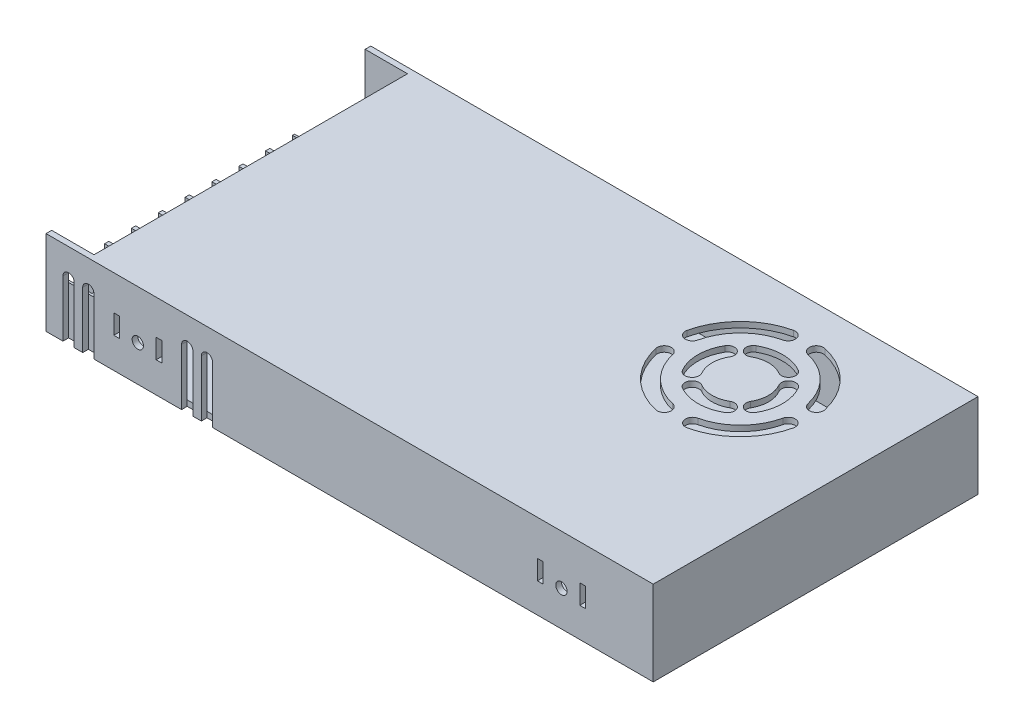
SolidWorks part; units mm, degrees
material "1060 Alloy"
ref_plane "Front Plane" through (0, 0, 0) normal (0, 0, 1) x (1, 0, 0)
ref_plane "Top Plane" through (0, 0, 0) normal (0, 1, 0) x (1, 0, 0)
ref_plane "Right Plane" through (0, 0, 0) normal (1, 0, 0) x (0, 0, -1)
sketch "Sketch1" plane through (0, 0, 0) normal (0, 1, 0) x (1, 0, 0)
  line L1 (107.5, -57.5) -> (-107.5, -57.5)
  line L2 (107.5, -57.5) -> (107.5, 57.5)
  line L3 (107.5, 57.5) -> (-107.5, 57.5)
  line L4 (-107.5, -57.5) -> (-107.5, 57.5)
  line L5 (107.5, -57.5) -> (-107.5, 57.5) construction
  line L6 (107.5, 57.5) -> (-107.5, -57.5) construction
  point P0 (0, 0)
  dimension "D1" = 215
  dimension "D2" = 115
extrude "Boss-Extrude1" add sketch "Sketch1" along normal blind 30
shell "Shell1" thickness 2
sketch "Sketch2" plane through (0, 30, 0) normal (0, 1, 0) x (1, 0, 0)
  line L0 (107.5, -57.5) -> (107.5, 57.5) construction
  line L1 (107.5, 57.5) -> (-107.5, 57.5) construction
  line L2 (60.05, 20.8) -> (14.6527, 20.8) construction
  line L4 (14.6527, 66.1973) -> (60.05, 20.8) construction
  circle A0 centre (60.05, 20.8) radius 12.5 construction
  circle A1 centre (60.05, 20.8) radius 22.5 construction
  arc A2 (53.8, 31.6253) -> (66.3, 31.6253) centre (60.05, 20.8) cw construction
  arc A3 (67.55, 33.7904) -> (52.55, 33.7904) centre (60.05, 20.8) ccw
  arc A4 (65.05, 29.4603) -> (55.05, 29.4603) centre (60.05, 20.8) ccw
  arc A5 (65.05, 29.4603) -> (67.55, 33.7904) centre (66.3, 31.6253) ccw
  arc A6 (52.55, 33.7904) -> (55.05, 29.4603) centre (53.8, 31.6253) ccw
  arc A7 (55.05, 42.7374) -> (38.1126, 25.8) centre (60.05, 20.8) ccw construction
  arc A8 (54.4944, 45.1749) -> (35.6751, 26.3556) centre (60.05, 20.8) ccw
  arc A9 (55.6056, 40.2999) -> (40.5501, 25.2444) centre (60.05, 20.8) ccw
  arc A10 (55.6056, 40.2999) -> (54.4944, 45.1749) centre (55.05, 42.7374) ccw
  arc A11 (35.6751, 26.3556) -> (40.5501, 25.2444) centre (38.1126, 25.8) ccw
  point P9 (60.05, 33.3)
  point P14 (44.1401, 36.7099)
  dimension "D3" = 25
  dimension "D4" = 15
  dimension "D5" = 5
  dimension "D6" = 45
  dimension "D7" = 5
  dimension "D1" = 47.45
  dimension "D2" = 36.7
  dimension "D8" = 45
  dimension "D9" = 5
extrude "Cut-Extrude1" cut sketch "Sketch2" against normal offset from surface (28 mm away) 2 up to face at (0, 0, 0)
pattern_circular "CirPattern1" count 4 over 360 about axis through (60.05, 0, -20.8) along (0, 1, 0) of "Cut-Extrude1"
sketch "Sketch3" plane through (0, 30, 0) normal (0, 1, 0) x (1, 0, 0)
  line L0 (-107.5, 57.5) -> (-107.5, -57.5) construction
  line L1 (-107.5, 55.5) -> (-92.5, 55.5)
  line L2 (-107.5, 55.5) -> (-107.5, -55.5)
  line L3 (-107.5, -55.5) -> (-92.5, -55.5)
  line L4 (-92.5, 55.5) -> (-92.5, -55.5)
  line L5 (107.5, 57.5) -> (-107.5, 57.5) construction
  line L6 (-107.5, -57.5) -> (107.5, -57.5) construction
  dimension "D1" = 2
  dimension "D2" = 2
  dimension "D3" = 15
extrude "Cut-Extrude2" cut sketch "Sketch3" against normal blind 10
sketch "Sketch4" plane through (0, 30, 0) normal (0, 1, 0) x (1, 0, 0)
  line L0 (107.5, -25) -> (-75, -25) construction
  line L1 (107.5, -57.5) -> (107.5, 57.5) construction
  line L2 (-75, -25) -> (-75, 25) construction
  line L3 (-75, 25) -> (107.5, 25) construction
  line L4 (-107.5, -57.5) -> (107.5, -57.5) construction
  line L5 (-107.5, 55.5) -> (-107.5, -55.5) construction
  circle A0 centre (-75, 25) radius 2
  circle A1 centre (-75, -25) radius 2
  circle A3 centre (75, -25) radius 2
  circle A4 centre (75, 25) radius 2
  dimension "D3" = 4
  dimension "D1" = 32.5
  dimension "D2" = 50
  dimension "D4" = 32.5
  dimension "D5" = 150
extrude "Cut-Extrude3" cut sketch "Sketch4" against normal through all from offset 20 offset against normal yes
sketch "Sketch5" plane through (0, 2, 0) normal (0, 1, 0) x (1, 0, 0)
  line L0 (-107, -55.5) -> (-107, -46)
  line L2 (-107, -46) -> (-92.5, -46)
  line L3 (-92.5, -55.5) -> (-92.5, 55.5) construction
  line L4 (-92.5, -46) -> (-92.5, -55.5)
  line L5 (-107.5, -55.5) -> (105.5, -55.5) construction
  line L6 (-92.5, -55.5) -> (-107, -55.5)
  line L7 (-107.5, 55.5) -> (-107.5, -55.5) construction
  dimension "D1" = 9.5
  dimension "D2" = 0.5
extrude "Boss-Extrude2" add sketch "Sketch5" along normal blind 15
sketch "Sketch6" plane through (0, 17, 0) normal (0, 1, 0) x (1, 0, 0)
  line L0 (-107, -46) -> (-107, -55.5) construction
  line L1 (-107, -46.75) -> (-94, -46.75)
  line L2 (-107, -46.75) -> (-107, -54.75)
  line L3 (-107, -54.75) -> (-94, -54.75)
  line L4 (-94, -46.75) -> (-94, -54.75)
  line L7 (-92.5, -55.5) -> (-92.5, 55.5) construction
  point P6 (-107, -50.75)
  dimension "D1" = 8
  dimension "D3" = 1.5
extrude "Cut-Extrude4" cut sketch "Sketch6" against normal blind 10
sketch "Sketch7" plane through (0, 7, 0) normal (0, 1, 0) x (1, 0, 0)
  line L0 (-107, -46.75) -> (-94, -54.75) construction
  line L1 (-94.5, -54.5) -> (-106.5, -54.5)
  line L2 (-94.5, -54.5) -> (-94.5, -47)
  line L3 (-94.5, -47) -> (-106.5, -47)
  line L4 (-106.5, -54.5) -> (-106.5, -47)
  line L5 (-94.5, -54.5) -> (-106.5, -47) construction
  line L6 (-94.5, -47) -> (-106.5, -54.5) construction
  point P0 (-100.5, -50.75)
  point P9 (-100.5, -50.75)
  dimension "D1" = 7.5
  dimension "D2" = 12
extrude "Boss-Extrude3" add sketch "Sketch7" along normal blind 1
sketch "Sketch8" plane through (0, 8, 0) normal (0, 1, 0) x (1, 0, 0)
  line L0 (-106.5, -47) -> (-94.5, -54.5) construction
  circle A0 centre (-100.5, -50.75) radius 3
  dimension "D1" = 6
extrude "Boss-Extrude4" add sketch "Sketch8" along normal blind 2
fillet "Fillet1" radius 1 1 edges at (-100.5, 10, 53.75)
pattern_linear "LPattern1" count 9 spacing 9.5 along (0, 0, -1) of "Fillet1", "Boss-Extrude4", "Boss-Extrude3", "Boss-Extrude2", "Cut-Extrude4"
sketch "Sketch9" plane through (0, 0, 57.5) normal (0, 0, 1) x (1, 0, 0)
  line L0 (-101.5, 0) -> (-101.5, 20)
  line L1 (-107.5, 0) -> (107.5, 0) construction
  line L2 (-97.5, 20) -> (-97.5, 0)
  line L3 (-97.5, 0) -> (-101.5, 0)
  line L4 (-94.5, 0) -> (-90.5, 0)
  line L5 (-90.5, 0) -> (-90.5, 20)
  line L6 (-94.5, 20) -> (-94.5, 0)
  line L7 (-59.5, 0) -> (-59.5, 20)
  line L8 (-55.5, 20) -> (-55.5, 0)
  line L9 (-55.5, 0) -> (-59.5, 0)
  line L10 (-52.5, 0) -> (-48.5, 0)
  line L11 (-48.5, 0) -> (-48.5, 20)
  line L12 (-52.5, 20) -> (-52.5, 0)
  line L13 (-107.5, 30) -> (-107.5, 0) construction
  line L15 (-81.5, 10.8) -> (-83.5, 10.8)
  line L16 (-81.5, 10.8) -> (-81.5, 17.7)
  line L17 (-81.5, 17.7) -> (-83.5, 17.7)
  line L18 (-83.5, 10.8) -> (-83.5, 17.7)
  line L19 (-81.5, 10.8) -> (-83.5, 17.7) construction
  line L20 (-81.5, 17.7) -> (-83.5, 10.8) construction
  line L21 (-66.5, 10.8) -> (-68.5, 10.8)
  line L22 (-66.5, 10.8) -> (-66.5, 17.7)
  line L23 (-66.5, 17.7) -> (-68.5, 17.7)
  line L24 (-68.5, 10.8) -> (-68.5, 17.7)
  line L25 (-66.5, 10.8) -> (-68.5, 17.7) construction
  line L26 (-66.5, 17.7) -> (-68.5, 10.8) construction
  line L27 (81.5, 10.5) -> (83.556, 10.5)
  line L28 (81.5, 10.5) -> (81.5, 17.4)
  line L29 (81.5, 17.4) -> (83.556, 17.4)
  line L30 (83.556, 10.5) -> (83.556, 17.4)
  line L31 (81.5, 10.5) -> (83.556, 17.4) construction
  line L32 (81.5, 17.4) -> (83.556, 10.5) construction
  line L33 (66.5, 10.5) -> (68.5, 10.5)
  line L34 (66.5, 10.5) -> (66.5, 17.4)
  line L35 (66.5, 17.4) -> (68.5, 17.4)
  line L36 (68.5, 10.5) -> (68.5, 17.4)
  line L37 (66.5, 10.5) -> (68.5, 17.4) construction
  line L38 (66.5, 17.4) -> (68.5, 10.5) construction
  circle A0 centre (-75, 12.8) radius 2
  circle A1 centre (75, 12.5) radius 2
  arc A2 (-101.5, 20) -> (-97.5, 20) centre (-99.5, 20) cw
  arc A3 (-90.5, 20) -> (-94.5, 20) centre (-92.5, 20) ccw
  arc A4 (-59.5, 20) -> (-55.5, 20) centre (-57.5, 20) cw
  arc A5 (-48.5, 20) -> (-52.5, 20) centre (-50.5, 20) ccw
  point P26 (82.528, 13.95)
  point P30 (-82.5, 14.25)
  point P36 (-67.5, 14.25)
  point P43 (67.5, 13.95)
  dimension "D8" = 4
  dimension "D16" = 4
  dimension "D1" = 6
  dimension "D2" = 3
  dimension "D3" = 20
  dimension "D4" = 4
  dimension "D5" = 2
  dimension "D6" = 6.5
  dimension "D7" = 32.5
  dimension "D9" = 12.8
  dimension "D10" = 6.9
  dimension "D11" = 6.5
  dimension "D12" = 7
  dimension "D13" = 3
  dimension "D14" = 150
  dimension "D15" = 12.5
  dimension "D17" = 6.5
  dimension "D18" = 6.5
extrude "Cut-Extrude5" cut sketch "Sketch9" against normal blind 2
mirror "Mirror2" about plane through (0, 0, 0) normal (0, 0, 1) of "Cut-Extrude5"
